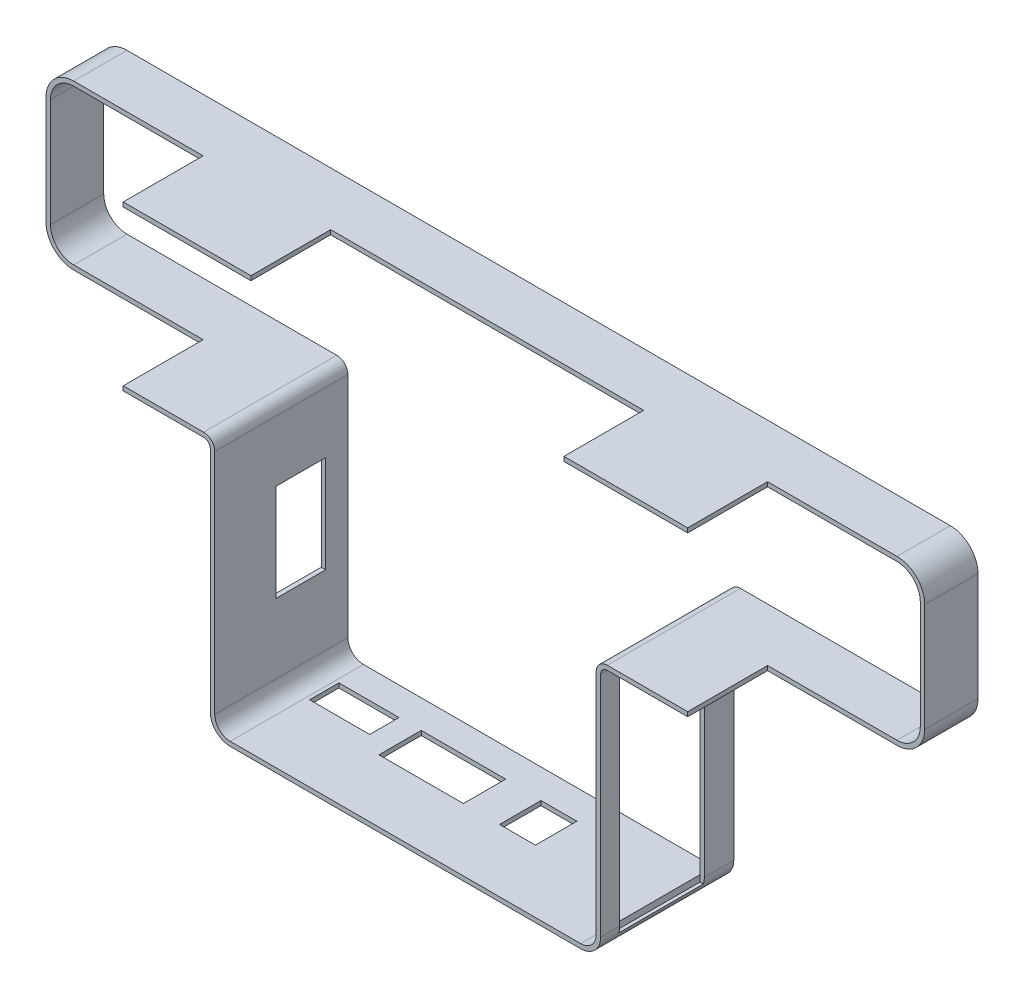
SolidWorks part; units mm, degrees
ref_plane "Ebene vorne" through (0, 0, 0) normal (0, 0, 1) x (1, 0, 0)
ref_plane "Ebene oben" through (0, 0, 0) normal (0, 1, 0) x (1, 0, 0)
ref_plane "Ebene rechts" through (0, 0, 0) normal (1, 0, 0) x (0, 0, -1)
sketch "Skizze2" plane through (0, 0, 188.6848) normal (0, 0, -1) x (-1, 0, 0)
  line L0 (114.2553, 56.8042) -> (-71.2025, 56.8042)
  line L1 (-23.9357, 21.9394) -> (-71.2025, 21.9394)
  line L2 (-76.4445, 27.1814) -> (-76.4445, 51.5622)
  line L3 (119.4973, 51.5622) -> (119.4973, 27.1814)
  line L4 (114.2553, 21.9394) -> (66.9885, 21.9394)
  line L5 (64.4885, 19.4394) -> (64.4885, -31.8652)
  line L6 (-21.4357, 19.4394) -> (-21.4357, -31.8652)
  line L7 (60.9885, -35.3652) -> (-17.9357, -35.3652)
  line L8 (114.2553, 57.8042) -> (-71.2025, 57.8042)
  line L9 (-71.2025, 56.3042) -> (114.2553, 56.3042) construction
  line L10 (-77.4445, 51.5622) -> (-77.4445, 27.1814)
  line L11 (-23.9357, 20.9394) -> (-71.2025, 20.9394)
  line L12 (-22.4357, 19.4394) -> (-22.4357, -31.8652)
  line L13 (-17.9357, -36.3652) -> (60.9885, -36.3652)
  line L14 (65.4885, -31.8652) -> (65.4885, 19.4394)
  line L15 (114.2553, 20.9394) -> (66.9885, 20.9394)
  line L16 (120.4973, 51.5622) -> (120.4973, 27.1814)
  arc A0 (114.2553, 56.8042) -> (119.4973, 51.5622) centre (114.2553, 51.5622) cw
  arc A1 (119.4973, 27.1814) -> (114.2553, 21.9394) centre (114.2553, 27.1814) cw
  arc A2 (66.9885, 21.9394) -> (64.4885, 19.4394) centre (66.9885, 19.4394) ccw
  arc A3 (64.4885, -31.8652) -> (60.9885, -35.3652) centre (60.9885, -31.8652) cw
  arc A4 (-21.4357, -31.8652) -> (-17.9357, -35.3652) centre (-17.9357, -31.8652) ccw
  arc A5 (-23.9357, 21.9394) -> (-21.4357, 19.4394) centre (-23.9357, 19.4394) cw
  arc A6 (-71.2025, 56.8042) -> (-76.4445, 51.5622) centre (-71.2025, 51.5622) ccw
  arc A7 (-71.2025, 21.9394) -> (-76.4445, 27.1814) centre (-71.2025, 27.1814) cw
  arc A8 (-71.2025, 57.8042) -> (-77.4445, 51.5622) centre (-71.2025, 51.5622) ccw
  arc A9 (-77.4445, 27.1814) -> (-71.2025, 20.9394) centre (-71.2025, 27.1814) ccw
  arc A10 (-23.9357, 20.9394) -> (-22.4357, 19.4394) centre (-23.9357, 19.4394) cw
  arc A11 (-22.4357, -31.8652) -> (-17.9357, -36.3652) centre (-17.9357, -31.8652) ccw
  arc A12 (60.9885, -36.3652) -> (65.4885, -31.8652) centre (60.9885, -31.8652) ccw
  arc A13 (65.4885, 19.4394) -> (66.9885, 20.9394) centre (66.9885, 19.4394) cw
  arc A14 (114.2553, 20.9394) -> (120.4973, 27.1814) centre (114.2553, 27.1814) ccw
  arc A15 (114.2553, 57.8042) -> (120.4973, 51.5622) centre (114.2553, 51.5622) cw
  dimension "D2" = 1
  dimension "D1" = 0.5
extrude "Aufsatz-Linear austragen1" add sketch "Skizze2" against normal blind 30
sketch "Skizze4" plane through (22.4357, 0, 0) normal (1, 0, 0) x (0, 0, -1)
  line L1 (-214.3789, 20.3073) -> (-195.3192, 20.3073)
  line L2 (-214.3789, 20.3073) -> (-214.3789, -33.2972)
  line L3 (-214.3789, -33.2972) -> (-195.3192, -33.2972)
  line L4 (-195.3192, 20.3073) -> (-195.3192, -33.2972)
extrude "Schnitt-Linear austragen1" cut sketch "Skizze4" against normal up to vertex (1 mm away)
sketch "Skizze5" plane through (0, -36.3652, 0) normal (0, -1, 0) x (1, 0, 0)
  line L0 (-60.1574, 201.8692) -> (-60.1574, 200.6692) construction
  line L1 (-60.1574, 201.6417) -> (-46.6221, 201.6417)
  line L2 (-60.1574, 201.6417) -> (-60.1574, 195.0433)
  line L3 (-60.1574, 195.0433) -> (-46.6221, 195.0433)
  line L4 (-46.6221, 201.6417) -> (-46.6221, 195.0433)
  line L5 (-22.2785, 204.5692) -> (-22.9185, 204.5692) construction
  line L6 (-41.6093, 195.0433) -> (-22.5985, 195.0433)
  line L7 (-41.6093, 195.0433) -> (-41.6093, 204.5692)
  line L8 (-41.6093, 204.5692) -> (-22.5985, 204.5692)
  line L9 (-22.5985, 195.0433) -> (-22.5985, 204.5692)
  line L10 (-14.3117, 195.2392) -> (-26.3537, 195.2392) construction
  line L11 (-14.4481, 195.2392) -> (-6.3663, 195.2392)
  line L12 (-14.4481, 195.2392) -> (-14.4481, 204.5692)
  line L13 (-14.4481, 204.5692) -> (-6.3663, 204.5692)
  line L14 (-6.3663, 195.2392) -> (-6.3663, 204.5692)
extrude "Schnitt-Linear austragen2" cut sketch "Skizze5" against normal up to vertex (1 mm away)
sketch "Skizze6" plane through (-65.4885, 0, 0) normal (-1, 0, 0) x (0, 0, 1)
  line L0 (197.4692, 5.734) -> (212.4092, 5.734) construction
  line L1 (204.9392, 5.734) -> (193.6848, 5.734)
  line L2 (204.9392, 5.734) -> (204.9392, -16.1447)
  line L3 (204.9392, -16.1447) -> (193.6848, -16.1447)
  line L4 (193.6848, 5.734) -> (193.6848, -16.1447)
  line L5 (193.6848, 19.4394) -> (193.6848, -31.8652) construction
ref_plane "Ebene1" through (-64.4885, 19.4394, 218.6848) normal (0, 1, 0) x (1, 0, 0)
extrude "Schnitt-Linear austragen3" cut sketch "Skizze6" against normal up to vertex (1 mm away)
sketch "Skizze8" plane through (0, 57.8042, 0) normal (0, 1, 0) x (1, 0, 0)
  line L0 (-56.3324, -224.0326) -> (-56.3324, -217.3826) construction
  line L1 (14.1676, -200.7265) -> (-56.3324, -200.7265)
  line L2 (14.1676, -200.7265) -> (14.1676, -219.5445)
  line L3 (14.1676, -219.5445) -> (-56.3324, -219.5445)
  line L4 (-56.3324, -200.7265) -> (-56.3324, -219.5445)
  line L5 (14.1676, -223.8826) -> (14.1676, -201.8826) construction
extrude "Schnitt-Linear austragen4" cut sketch "Skizze8" against normal up to vertex (1 mm away)
sketch "Skizze9" plane through (0, 0, 218.6848) normal (0, 0, 1) x (1, 0, 0)
  line L0 (77.4445, 51.5622) -> (77.4445, 27.1814)
  line L1 (71.2025, 20.9394) -> (42.0463, 20.9394)
  line L2 (71.2025, 20.9394) -> (23.9357, 20.9394) construction
  line L3 (42.0463, 20.9394) -> (42.0463, 57.8042)
  line L4 (14.1676, 57.8042) -> (71.2025, 57.8042) construction
  line L5 (42.0463, 57.8042) -> (71.2025, 57.8042)
  line L6 (-21.5264, -56.5979) -> (-21.5264, 95.4538) construction
  line L7 (75.9445, 27.1814) -> (75.9445, 51.5622) construction
  line L8 (-118.9973, 51.5622) -> (-118.9973, 27.1814) construction
  line L9 (-85.0991, 57.8042) -> (-85.0991, 20.9394)
  line L10 (-114.2553, 57.8042) -> (-56.3324, 57.8042) construction
  line L11 (-66.9885, 20.9394) -> (-114.2553, 20.9394) construction
  line L12 (-85.0991, 20.9394) -> (-114.2553, 20.9394)
  line L13 (-85.0991, 57.8042) -> (-114.2553, 57.8042)
  line L14 (-120.4973, 27.1814) -> (-120.4973, 51.5622)
  arc A0 (77.4445, 27.1814) -> (71.2025, 20.9394) centre (71.2025, 27.1814) cw
  arc A1 (71.2025, 57.8042) -> (77.4445, 51.5622) centre (71.2025, 51.5622) cw
  arc A2 (-114.2553, 57.8042) -> (-120.4973, 51.5622) centre (-114.2553, 51.5622) ccw
  arc A3 (-114.2553, 20.9394) -> (-120.4973, 27.1814) centre (-114.2553, 27.1814) cw
extrude "Schnitt-Linear austragen5" cut sketch "Skizze9" against normal blind 18
sketch "Skizze10" plane through (0, 0, 221.6848) normal (0, 0, 1) x (1, 0, 0)
  line L0 (-21.5264, 69.0336) -> (-21.5264, -63.3248) construction
  line L1 (21.4357, 19.4394) -> (21.4357, -31.8652) construction
  line L2 (-64.4885, -31.8652) -> (-64.4885, 19.4394) construction
  line L3 (-41.4172, 8.2135) -> (-1.6356, 8.2135)
  line L4 (-40.1965, 10.2135) -> (-2.8564, 10.2135)
  line L5 (-40.1965, 10.2135) -> (-40.1965, 9.2135)
  line L6 (-40.1965, 9.2135) -> (-2.8564, 9.2135)
  line L7 (-2.8564, 10.2135) -> (-2.8564, 9.2135)
  line L8 (-41.4172, 8.2135) -> (-41.4172, 7.2135)
  line L9 (-41.4172, 7.2135) -> (-1.6356, 7.2135)
  line L10 (-1.6356, 8.2135) -> (-1.6356, 7.2135)
  line L11 (-43.1085, 4.2135) -> (0.0557, 4.2135)
  line L12 (-42.3762, 6.2135) -> (-0.6766, 6.2135)
  line L13 (-42.3762, 6.2135) -> (-42.3762, 5.2135)
  line L14 (-42.3762, 5.2135) -> (-0.6766, 5.2135)
  line L15 (-0.6766, 6.2135) -> (-0.6766, 5.2135)
  line L16 (-43.1085, 4.2135) -> (-43.1085, 3.2135)
  line L17 (-43.1085, 3.2135) -> (0.0557, 3.2135)
  line L18 (0.0557, 4.2135) -> (0.0557, 3.2135)
  line L19 (-43.9748, 0.2135) -> (0.922, 0.2135)
  line L20 (-43.6366, 2.2135) -> (0.5837, 2.2135)
  line L21 (-43.6366, 2.2135) -> (-43.6366, 1.2135)
  line L22 (-43.6366, 1.2135) -> (0.5837, 1.2135)
  line L23 (0.5837, 2.2135) -> (0.5837, 1.2135)
  line L24 (-43.9748, 0.2135) -> (-43.9748, -0.7865)
  line L25 (-43.9748, -0.7865) -> (0.922, -0.7865)
  line L26 (0.922, 0.2135) -> (0.922, -0.7865)
  line L27 (-44.1112, -3.7865) -> (1.0584, -3.7865)
  line L28 (-44.1318, -1.7865) -> (1.079, -1.7865)
  line L29 (-44.1318, -1.7865) -> (-44.1318, -2.7865)
  line L30 (-44.1318, -2.7865) -> (1.079, -2.7865)
  line L31 (1.079, -1.7865) -> (1.079, -2.7865)
  line L32 (-44.1112, -3.7865) -> (-44.1112, -4.7865)
  line L33 (-44.1112, -4.7865) -> (1.0584, -4.7865)
  line L34 (1.0584, -3.7865) -> (1.0584, -4.7865)
  line L35 (-43.9127, -5.7865) -> (0.8599, -5.7865)
  line L36 (-43.9127, -5.7865) -> (-43.9127, -6.7865)
  line L37 (-43.9127, -6.7865) -> (0.8599, -6.7865)
  line L38 (0.8599, -5.7865) -> (0.8599, -6.7865)
  line L39 (-42.9575, -9.7865) -> (-0.0953, -9.7865)
  line L40 (-43.5314, -7.7865) -> (0.4786, -7.7865)
  line L41 (-43.5314, -7.7865) -> (-43.5314, -8.7865)
  line L42 (-43.5314, -8.7865) -> (0.4786, -8.7865)
  line L43 (0.4786, -7.7865) -> (0.4786, -8.7865)
  line L44 (-42.9575, -9.7865) -> (-42.9575, -10.7865)
  line L45 (-42.9575, -10.7865) -> (-0.0953, -10.7865)
  line L46 (-0.0953, -9.7865) -> (-0.0953, -10.7865)
  line L47 (-41.1589, -13.7865) -> (-3.3376, -13.7865)
  line L48 (-42.175, -11.7865) -> (-0.8778, -11.7865)
  line L49 (-42.175, -11.7865) -> (-42.175, -12.7865)
  line L50 (-42.175, -12.7865) -> (-0.8778, -12.7865)
  line L51 (-0.8778, -11.7865) -> (-0.8778, -12.7865)
  line L52 (-41.1589, -13.7865) -> (-41.1589, -14.7865)
  line L53 (-41.1589, -14.7865) -> (-3.3376, -14.7865)
  line L54 (-3.3376, -13.7865) -> (-3.3376, -14.7865)
  line L55 (-38.247, -17.7865) -> (-4.8058, -17.7865)
  line L56 (-39.8705, -15.7865) -> (-3.1823, -15.7865)
  line L57 (-39.8705, -15.7865) -> (-39.8705, -16.7865)
  line L58 (-39.8705, -16.7865) -> (-3.1823, -16.7865)
  line L59 (-3.1823, -15.7865) -> (-3.1823, -16.7865)
  line L60 (-38.247, -17.7865) -> (-38.247, -18.7865)
  line L61 (-38.247, -18.7865) -> (-4.8058, -18.7865)
  line L62 (-4.8058, -17.7865) -> (-4.8058, -18.7865)
  line L63 (-38.6582, 12.2135) -> (-4.3946, 12.2135)
  line L64 (-34.0884, 16.2548) -> (-8.9644, 16.2548)
  line L65 (-34.0884, 16.2548) -> (-34.0884, 15.2548)
  line L66 (-34.0884, 15.2548) -> (-8.9644, 15.2548)
  line L67 (-8.9644, 16.2548) -> (-8.9644, 15.2548)
  line L68 (-38.6582, 12.2135) -> (-38.6582, 11.2135)
  line L69 (-38.6582, 11.2135) -> (-4.3946, 11.2135)
  line L70 (-4.3946, 12.2135) -> (-4.3946, 11.2135)
  line L71 (-36.6605, 14.2548) -> (-6.3923, 14.2548)
  line L72 (-30.3902, 18.2548) -> (-12.6626, 18.2548)
  line L73 (-30.3902, 18.2548) -> (-30.3902, 17.2548)
  line L74 (-30.3902, 17.2548) -> (-12.6626, 17.2548)
  line L75 (-12.6626, 18.2548) -> (-12.6626, 17.2548)
  line L76 (-36.6605, 14.2548) -> (-36.6605, 13.2548)
  line L77 (-36.6605, 13.2548) -> (-6.3923, 13.2548)
  line L78 (-6.3923, 14.2548) -> (-6.3923, 13.2548)
  line L79 (-33.4311, -21.7865) -> (-9.6217, -21.7865)
  line L80 (-36.1774, -19.7865) -> (-6.8754, -19.7865)
  line L81 (-36.1774, -19.7865) -> (-36.1774, -20.7865)
  line L82 (-36.1774, -20.7865) -> (-6.8754, -20.7865)
  line L83 (-6.8754, -19.7865) -> (-6.8754, -20.7865)
  line L84 (-33.4311, -21.7865) -> (-33.4311, -22.7865)
  line L85 (-33.4311, -22.7865) -> (-9.6217, -22.7865)
  line L86 (-9.6217, -21.7865) -> (-9.6217, -22.7865)
  point P8 (-39.018, 9.0391)
  point P13 (0, 0)
  point P94 (0, 0)
  point P95 (-30.6446, 18.1446)
  point P96 (0, 0)
  point P97 (-12.6626, 17.5158)
  point P98 (0, 0)
  point P99 (0, 0)
  point P100 (0, 0)
  point P101 (-32.4371, 17.2583)
  point P102 (-33.1429, 15.9253)
  point P103 (-35.1685, 15.4867)
  point P104 (-7.6876, 15.3363)
  point P105 (-7.3112, 14.1844)
  point P106 (-37.3776, 13.5803)
  point P107 (-5.5232, 13.4296)
  point P108 (-37.4247, 12.6317)
  point P109 (-38.9407, 11.8794)
  point P110 (-40.2949, 10.0684)
  point P111 (-2.8883, 10.2601)
  point P112 (-42.0828, 6.8808)
  point P113 (-43.1328, 4.1354)
  point P114 (-43.634, 2.2253)
  point P115 (-43.9965, 0.0314)
  point P116 (-44.1438, -2.3447)
  point P117 (-44.0603, -4.5079)
  point P118 (-43.7708, -6.651)
  point P119 (-43.3585, -8.4664)
  point P120 (-42.6887, -10.5389)
  point P121 (-41.7309, -12.7216)
  point P122 (-40.6073, -14.6999)
  point P123 (-39.1195, -16.7699)
  point P124 (-37.1421, -18.9174)
  point P125 (-34.5388, -21.0551)
  point P126 (-31.368, -22.9196)
  point P127 (-0.9896, 6.9235)
  point P128 (0.0912, 4.0991)
  point P129 (0.5606, 2.3197)
  point P130 (0.9473, 0)
  point P131 (1.0907, -2.3141)
  point P132 (1.0122, -4.4528)
  point P133 (0.7768, -6.3177)
  point P134 (0.4191, -8.0307)
  point P135 (-0.3965, -10.6241)
  point P136 (-1.3079, -12.6939)
  point P137 (-3.6813, -16.4522)
  point P138 (-6.0699, -19.0678)
  point P139 (-8.3715, -20.954)
  point P140 (-11.672, -22.9134)
  dimension "D1" = 1
  dimension "D2" = 1
  dimension "D3" = 1
  dimension "D4" = 1.0413
  dimension "D5" = 1
  dimension "D6" = 1
  dimension "D7" = 1
  dimension "D8" = 1
  dimension "D9" = 1
  dimension "D10" = 1
  dimension "D11" = 1
  dimension "D12" = 1
  dimension "D13" = 1
  dimension "D14" = 1
  dimension "D15" = 1
  dimension "D16" = 1
  dimension "D17" = 1
  dimension "D18" = 1
  dimension "D19" = 1
  dimension "D20" = 1
  dimension "D21" = 1
